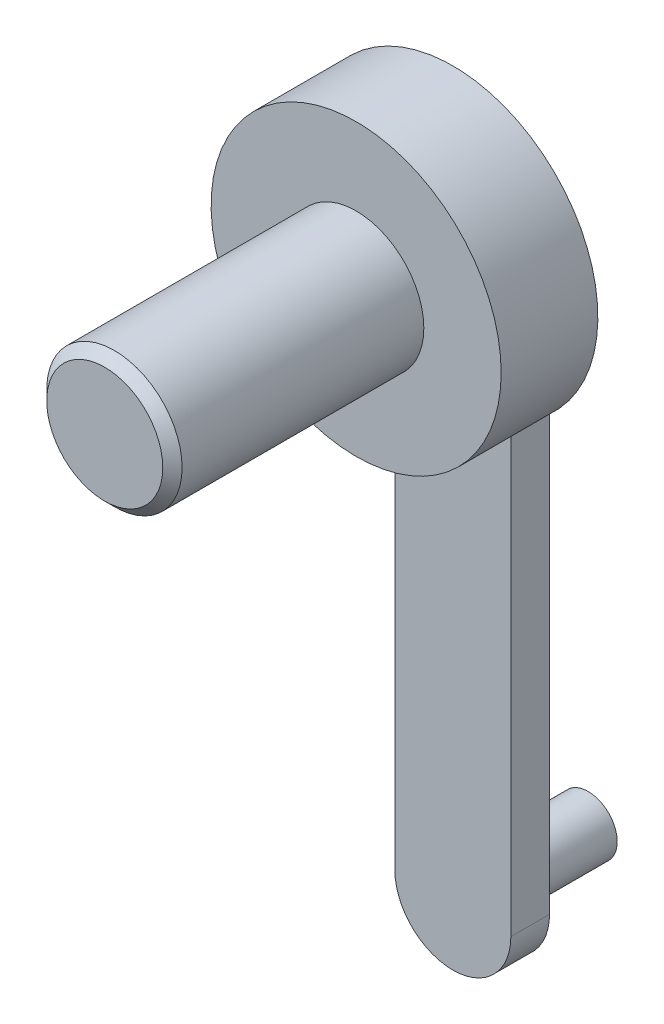
SolidWorks part; units mm, degrees
ref_plane "Front Plane" through (0, 0, 0) normal (0, 0, 1) x (1, 0, 0)
ref_plane "Top Plane" through (0, 0, 0) normal (0, 1, 0) x (1, 0, 0)
ref_plane "Right Plane" through (0, 0, 0) normal (1, 0, 0) x (0, 0, -1)
sketch "Sketch1" plane through (0, 0, 0) normal (0, 0, 1) x (1, 0, 0)
  circle A0 centre (0, 0) radius 7.5
  dimension "D1" = 15
extrude "Boss-Extrude1" add sketch "Sketch1" along normal blind 5
sketch "Sketch2" plane through (0, 0, 5) normal (0, 0, 1) x (1, 0, 0)
  circle A0 centre (0, 0) radius 3.5
  dimension "D1" = 7
extrude "Boss-Extrude2" add sketch "Sketch2" along normal blind 13
chamfer "Chamfer1" distance 0.5 angle 45 1 edges at (3.5, 0, 18)
sketch "Sketch3" plane through (0, 0, 0) normal (0, 0, -1) x (-1, 0, 0)
  line L0 (0, 0) -> (0, -30) construction
  line L1 (3, 0) -> (3, -30)
  line L2 (-3, 0) -> (-3, -30)
  arc A0 (3, 0) -> (-3, 0) centre (0, 0) ccw
  arc A1 (-3, -30) -> (3, -30) centre (0, -30) ccw
  point P3 (0, -15)
  dimension "D2" = 3
  dimension "D1" = 30
extrude "Boss-Extrude3" add sketch "Sketch3" along normal blind 2
sketch "Sketch4" plane through (0, 0, -2) normal (0, 0, -1) x (-1, 0, 0)
  circle A0 centre (0, -30) radius 1.5
  dimension "D1" = 3
extrude "Boss-Extrude4" add sketch "Sketch4" along normal blind 5
